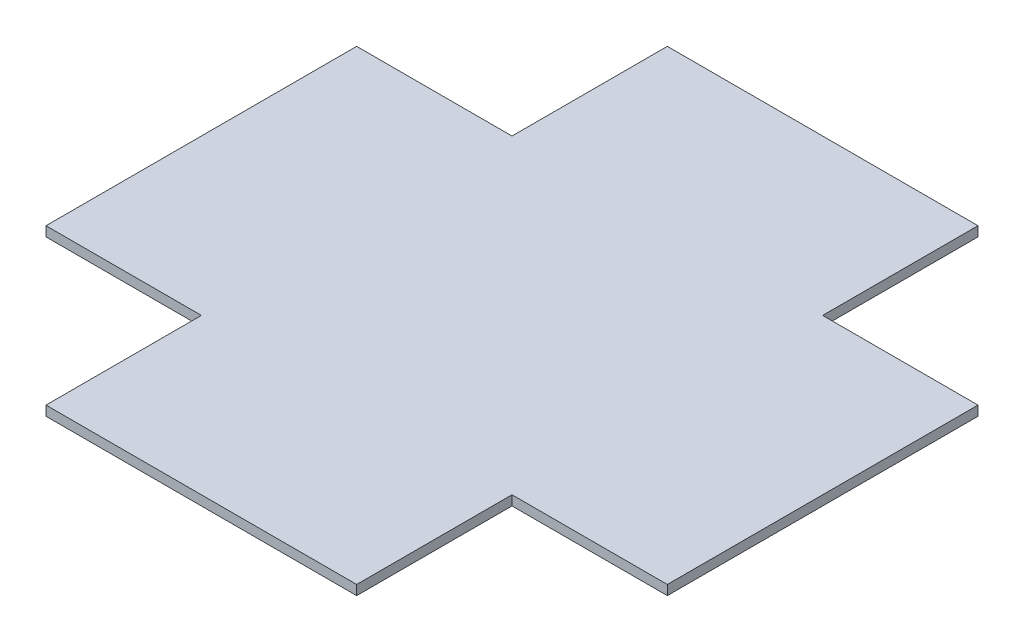
SolidWorks part; units mm, degrees
ref_plane "Front Plane" through (0, 0, 0) normal (0, 0, 1) x (1, 0, 0)
ref_plane "Top Plane" through (0, 0, 0) normal (0, 1, 0) x (1, 0, 0)
ref_plane "Right Plane" through (0, 0, 0) normal (1, 0, 0) x (0, 0, -1)
sketch "Sketch1" plane through (0, 0, 0) normal (0, 1, 0) x (1, 0, 0)
  line L0 (-25.4, 50.8) -> (-25.4, 25.4)
  line L1 (-25.4, 25.4) -> (-50.8, 25.4)
  line L2 (-50.8, 25.4) -> (-50.8, -25.4)
  line L3 (-50.8, -25.4) -> (-25.4, -25.4)
  line L4 (-25.4, -25.4) -> (-25.4, -50.8)
  line L5 (-25.4, -50.8) -> (25.4, -50.8)
  line L6 (25.4, -50.8) -> (25.4, -25.4)
  line L7 (25.4, -25.4) -> (50.8, -25.4)
  line L8 (50.8, -25.4) -> (50.8, 25.4)
  line L9 (50.8, 25.4) -> (25.4, 25.4)
  line L10 (25.4, 25.4) -> (25.4, 50.8)
  line L11 (25.4, 50.8) -> (-25.4, 50.8)
  dimension "D1" = 50.8
  dimension "D2" = 101.6
  dimension "D3" = 50.8
  dimension "D4" = 50.8
extrude "Boss-Extrude1" add sketch "Sketch1" along normal blind 1.5875
